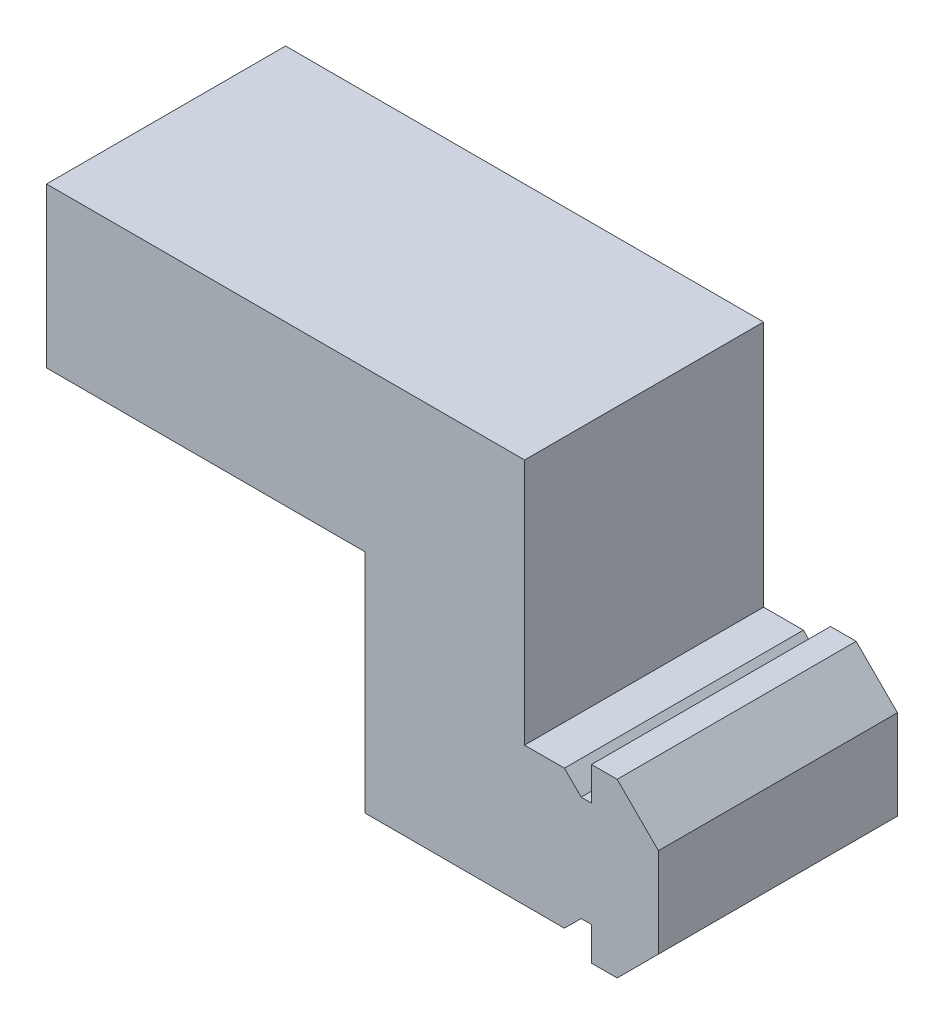
SolidWorks part; units mm, degrees
ref_plane "Front Plane" through (0, 0, 0) normal (0, 0, 1) x (1, 0, 0)
ref_plane "Top Plane" through (0, 0, 0) normal (0, 1, 0) x (1, 0, 0)
ref_plane "Right Plane" through (0, 0, 0) normal (1, 0, 0) x (0, 0, -1)
sketch "Sketch1" plane through (0, 0, 0) normal (0, 0, 1) x (1, 0, 0)
  line L0 (-3.6658, 8.0945) -> (-2.6158, 7.0445)
  line L1 (-1.9658, 7.0445) -> (-2.6158, 7.0445)
  line L2 (-1.9658, 7.0445) -> (-1.9658, 9.1445)
  line L3 (-1.9658, 9.1445) -> (-0.3547, 9.1445)
  line L4 (2.2342, 6.5556) -> (-0.3547, 9.1445)
  line L5 (2.2342, 6.5556) -> (2.2342, 0.9334)
  line L6 (2.2342, 0.9334) -> (-0.3547, -1.6555)
  line L7 (-1.9658, -1.6555) -> (-0.3547, -1.6555)
  line L8 (-1.9658, -1.6555) -> (-1.9658, 0.4445)
  line L9 (-1.9658, 0.4445) -> (-2.6158, 0.4445)
  line L10 (-2.6158, 0.4445) -> (-3.6658, -0.6055)
  line L11 (-3.6658, -0.6055) -> (-3.6658, 8.0945)
  line L12 (-3.6658, 3.7445) -> (2.2342, 3.7445) construction
  line L13 (-2.6158, 7.0445) -> (-2.6158, 0.4445) construction
  point P14 (-2.2908, 7.0445)
  point P15 (-0.7158, 3.7445)
  line B0 (6.1907, 3.7445) -> (-3.8093, 3.7445) construction
  line B1 (2.5007, 3.7445) -> (2.2907, 3.5345)
  line B2 (2.2907, 3.5345) -> (2.2907, 0.9052)
  line B3 (2.2907, 0.9052) -> (-0.3699, -1.7555)
  line B4 (-0.3699, -1.7555) -> (-2.0093, -1.7555)
  line B5 (-2.0093, -1.7555) -> (-2.0093, 0.3495)
  line B6 (-2.0093, 0.3495) -> (-2.6243, 0.3495)
  line B7 (-2.6243, 0.3495) -> (-3.8093, -0.8355)
  line B8 (-3.8093, -0.8355) -> (-3.8093, 8.3245)
  line B9 (6.1907, 3.7445) -> (0.2776, -2.1687) construction
  line B10 (-2.6243, 7.1395) -> (-3.8093, 8.3245)
  line B11 (-2.0093, 7.1395) -> (-2.6243, 7.1395)
  line B12 (-2.0093, 9.2445) -> (-2.0093, 7.1395)
  line B13 (-0.3699, 9.2445) -> (-2.0093, 9.2445)
  line B14 (2.2907, 6.5838) -> (-0.3699, 9.2445)
  line B15 (2.2907, 3.9545) -> (2.2907, 6.5838)
  line B16 (2.5007, 3.7445) -> (2.2907, 3.9545)
  dimension "D1" = 45
  dimension "D2" = 45
  dimension "D3" = 10.8
  dimension "D4" = 4.2
  dimension "D5" = 6.6
  dimension "D6" = 1.7
  dimension "D7" = 135
  dimension "D8" = 8.7
sketch_block_instance "V Slot 2-7"
sketch_block "V Slot 2" parameters "D1"=10, "D2"=11, "D3"=4.3, "D4"=1.8, "D5"=0.21, "D6"=45, "D7"=9.16, "D8"=1.5, "D9"=6.79, "D10"=3.7627
extrude "Boss-Extrude1" add sketch "Sketch1" along normal blind 15 contours L11 L10 L9 L8 L7 L6 L5 L4 L3 L2 L1 L0
sketch "Sketch2" plane through (-3.6658, 0, 0) normal (-1, 0, 0) x (0, 0, 1)
  line L0 (15, 8.0945) -> (0, 8.0945) construction
  line L1 (0, 8.0945) -> (15, 8.0945)
  line L2 (0, 8.0945) -> (0, -0.6055)
  line L3 (0, -0.6055) -> (15, -0.6055)
  line L4 (15, 8.0945) -> (15, -0.6055)
  line L7 (0, -0.6055) -> (0, 8.0945) construction
  point P12 (0, 3.7445)
extrude "Boss-Extrude2" add sketch "Sketch2" along normal blind 12.5
sketch "Sketch3" plane through (0, 8.0945, 0) normal (0, 1, 0) x (1, 0, 0)
  line L0 (-16.1658, 0) -> (-3.6658, 0) construction
  line L1 (-16.1658, -15) -> (-6.1658, -15)
  line L2 (-16.1658, -15) -> (-16.1658, 0)
  line L3 (-16.1658, 0) -> (-6.1658, 0)
  line L4 (-6.1658, -15) -> (-6.1658, 0)
  dimension "D1" = 10
extrude "Boss-Extrude3" add sketch "Sketch3" along normal blind 15.5
sketch "Sketch5" plane through (-16.1658, 0, 0) normal (-1, 0, 0) x (0, 0, 1)
  line L0 (15, -0.6055) -> (15, 23.5945) construction
  line L1 (0, 23.5945) -> (15, 23.5945)
  line L2 (0, 23.5945) -> (0, 13.5945)
  line L3 (0, 13.5945) -> (15, 13.5945)
  line L4 (15, 23.5945) -> (15, 13.5945)
  dimension "D1" = 10
extrude "Boss-Extrude4" add sketch "Sketch5" along normal blind 20
